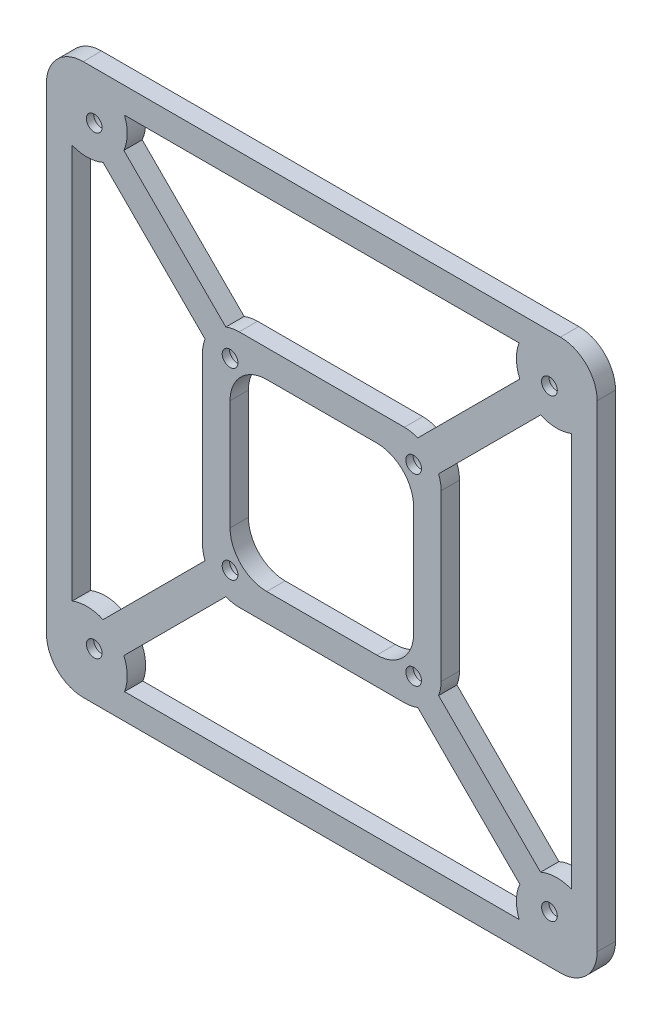
SolidWorks part; units mm, degrees
ref_plane "Front Plane" through (0, 0, 0) normal (0, 0, 1) x (1, 0, 0)
ref_plane "Top Plane" through (0, 0, 0) normal (0, 1, 0) x (1, 0, 0)
ref_plane "Right Plane" through (0, 0, 0) normal (1, 0, 0) x (0, 0, -1)
sketch "Sketch1" plane through (0, 0, 0) normal (0, 0, 1) x (1, 0, 0)
  circle A0 centre (-64, -64) radius 11
  circle A1 centre (-64, 64) radius 11
  circle A2 centre (64, -64) radius 11
  circle A3 centre (64, 64) radius 11
extrude "Boss-Extrude1" add sketch "Sketch1" along normal blind 5
sketch "Sketch2" plane through (0, 0, 0) normal (0, 0, 1) x (1, 0, 0)
  line L0 (-64, -64) -> (-84.1564, -84.1564) construction
  line L2 (-57.636, -70.364) -> (-77.7924, -90.5204)
  line L6 (-64, 64) -> (-81.1916, 81.1916) construction
  line L9 (-70.364, -57.636) -> (-90.5204, -77.7924)
  line L12 (-70.364, 57.636) -> (-87.5556, 74.8277)
  line L13 (-57.636, 70.364) -> (-74.8277, 87.5556)
  line L14 (64, -64) -> (80.8966, -80.8966) construction
  line L15 (70.364, -57.636) -> (87.2605, -74.5326)
  line L16 (57.636, -70.364) -> (74.5326, -87.2605)
  line L17 (64, 64) -> (83.0973, 83.0973) construction
  line L18 (57.636, 70.364) -> (76.7333, 89.4612)
  line L19 (70.364, 57.636) -> (89.4612, 76.7333)
  arc A13 (-70.364, 57.636) -> (-57.636, 70.364) centre (-64, 64) ccw
  arc A14 (-74.8277, 87.5556) -> (-87.5556, 74.8277) centre (-81.1916, 81.1916) ccw
  arc A15 (-57.636, -70.364) -> (-70.364, -57.636) centre (-64, -64) ccw
  arc A16 (-90.5204, -77.7924) -> (-77.7924, -90.5204) centre (-84.1564, -84.1564) ccw
  arc A17 (70.364, -57.636) -> (57.636, -70.364) centre (64, -64) ccw
  arc A18 (74.5326, -87.2605) -> (87.2605, -74.5326) centre (80.8966, -80.8966) ccw
  arc A19 (57.636, 70.364) -> (70.364, 57.636) centre (64, 64) ccw
  arc A20 (89.4612, 76.7333) -> (76.7333, 89.4612) centre (83.0973, 83.0973) ccw
  point P2 (-72.5958, 72.5958)
  point P3 (-74.0782, -74.0782)
  point P12 (72.4483, -72.4483)
  point P19 (73.5486, 73.5486)
sketch "Sketch3" plane through (0, 0, 0) normal (0, 0, 1) x (1, 0, 0)
  line L1 (-75, -75) -> (75, -75)
  line L2 (-75, -75) -> (-75, 75)
  line L3 (-75, 75) -> (75, 75)
  line L4 (75, -75) -> (75, 75)
  line L5 (-75, -75) -> (75, 75) construction
  line L6 (-75, 75) -> (75, -75) construction
  line L11 (73.1762, 73.1762) -> (-73.1762, -73.1762) construction
  line L12 (73.1762, -73.1762) -> (-73.1762, 73.1762) construction
  line L17 (70.0994, 70.0994) -> (-70.0994, -70.0994) construction
  line L18 (70.0994, -70.0994) -> (-70.0994, 70.0994) construction
  line L19 (68, 68) -> (-68, 68)
  line L20 (68, 68) -> (68, -68)
  line L21 (68, -68) -> (-68, -68)
  line L22 (-68, 68) -> (-68, -68)
  line L23 (68, 68) -> (-68, -68) construction
  line L24 (68, -68) -> (-68, 68) construction
  point P0 (0, 0)
  point P5 (0, 0)
  point P11 (0, 0)
  point P13 (0, 0)
sketch "Sketch8" plane through (0, 0, 0) normal (0, 0, 1) x (1, 0, 0)
  circle A4 centre (-62, 62) radius 2.14
  circle A5 centre (-62, -62) radius 2.14
  circle A6 centre (62, 62) radius 2.14
  circle A7 centre (62, -62) radius 2.14
extrude "Boss-Extrude3" add sketch "Sketch3" along normal blind 5
extrude "Boss-Extrude4" add sketch "Sketch8" along normal up to surface (5 mm away) separate body up to face at (7.0141, 7.0141, 5)
fillet "Fillet1" radius 10 4 edges at (75, -75, 2.5) (75, 75, 2.5) (-75, 75, 2.5) (-75, -75, 2.5)
combine bodies "Combine1" operation type add bodies to combine 136 101
sketch "Sketch9" plane through (0, 0, 0) normal (0, 0, 1) x (1, 0, 0)
  circle A4 centre (-62, 62) radius 4
  circle A5 centre (-62, -62) radius 4
  circle A6 centre (62, 62) radius 4
  circle A7 centre (62, -62) radius 4
extrude "Boss-Extrude5" add sketch "Sketch9" along normal blind 3 separate body
sketch "Sketch10" plane through (0, 0, 0) normal (0, 0, 1) x (1, 0, 0)
  line L1 (-25, -25) -> (25, -25)
  line L2 (-25, -25) -> (-25, 25)
  line L3 (-25, 25) -> (25, 25)
  line L4 (25, -25) -> (25, 25)
  line L5 (-25, -25) -> (25, 25) construction
  line L6 (-25, 25) -> (25, -25) construction
  line L7 (-32.5, -32.5) -> (32.5, -32.5)
  line L8 (-32.5, -32.5) -> (-32.5, 32.5)
  line L9 (-32.5, 32.5) -> (32.5, 32.5)
  line L10 (32.5, -32.5) -> (32.5, 32.5)
  line L11 (-32.5, -32.5) -> (32.5, 32.5) construction
  line L12 (-32.5, 32.5) -> (32.5, -32.5) construction
  point P0 (0, 0)
  point P6 (0, 0)
extrude "Boss-Extrude6" add sketch "Sketch10" along normal up to surface (5 mm away) separate body up to face at (0, 0, 5)
fillet "Fillet2" radius 10 8 edges at (32.5, -32.5, 2.5) (32.5, 32.5, 2.5) (25, 25, 2.5) (25, -25, 2.5) (-25, -25, 2.5) (-32.5, -32.5, 2.5) (-32.5, 32.5, 2.5) (-25, 25, 2.5)
sketch "Sketch11" plane through (0, 0, 0) normal (0, 0, 1) x (1, 0, 0)
  circle A6 centre (25, 25) radius 2.14
  circle A8 centre (-25, 25) radius 2.14
  circle A9 centre (-25, -25) radius 2.14
  circle A10 centre (25, -25) radius 2.14
  point P0 (0, 0)
extrude "Boss-Extrude7" add sketch "Sketch11" along normal up to surface (5 mm away) separate body up to face at (0, 0, 5)
sketch "Sketch12" plane through (0, 0, 0) normal (0, 0, 1) x (1, 0, 0)
  circle A6 centre (25, 25) radius 3.8
  circle A8 centre (-25, 25) radius 3.8
  circle A9 centre (-25, -25) radius 3.8
  circle A10 centre (25, -25) radius 3.8
  point P0 (0, 0)
extrude "Boss-Extrude8" add sketch "Sketch12" along normal blind 3 separate body
sketch "Sketch14" plane through (0, 0, 0) normal (0, 0, 1) x (1, 0, 0)
  line L0 (-62, 62) -> (-25, 25) construction
  line L1 (-59.1716, 64.8284) -> (-22.1716, 27.8284)
  line L2 (-64.8284, 59.1716) -> (-27.8284, 22.1716)
  line L3 (62, 62) -> (25, 25) construction
  line L4 (64.8284, 59.1716) -> (27.8284, 22.1716)
  line L5 (59.1716, 64.8284) -> (22.1716, 27.8284)
  line L6 (25, -25) -> (62, -62) construction
  line L7 (27.8284, -22.1716) -> (64.8284, -59.1716)
  line L8 (22.1716, -27.8284) -> (59.1716, -64.8284)
  line L9 (-25, -25) -> (-62, -62) construction
  line L10 (-22.1716, -27.8284) -> (-59.1716, -64.8284)
  line L11 (-27.8284, -22.1716) -> (-64.8284, -59.1716)
  arc A0 (-59.1716, 64.8284) -> (-64.8284, 59.1716) centre (-62, 62) ccw
  arc A1 (-27.8284, 22.1716) -> (-22.1716, 27.8284) centre (-25, 25) ccw
  arc A2 (64.8284, 59.1716) -> (59.1716, 64.8284) centre (62, 62) ccw
  arc A3 (22.1716, 27.8284) -> (27.8284, 22.1716) centre (25, 25) ccw
  arc A4 (27.8284, -22.1716) -> (22.1716, -27.8284) centre (25, -25) ccw
  arc A5 (59.1716, -64.8284) -> (64.8284, -59.1716) centre (62, -62) ccw
  arc A6 (-22.1716, -27.8284) -> (-27.8284, -22.1716) centre (-25, -25) ccw
  arc A7 (-64.8284, -59.1716) -> (-59.1716, -64.8284) centre (-62, -62) ccw
  point P4 (-43.5, 43.5)
  point P13 (43.5, 43.5)
  point P22 (43.5, -43.5)
  point P31 (-43.5, -43.5)
extrude "Boss-Extrude9" add sketch "Sketch14" along normal up to surface (5 mm away) separate body up to face at (0, 0, 5)
combine bodies "Combine4" operation type add bodies to combine 163 162 161 160 142 149
combine bodies "Combine5" operation type subtract main body 164 bodies to subtract 158 157 156 155 154 153 152 151 147 146 145 144 141 140 139 138
